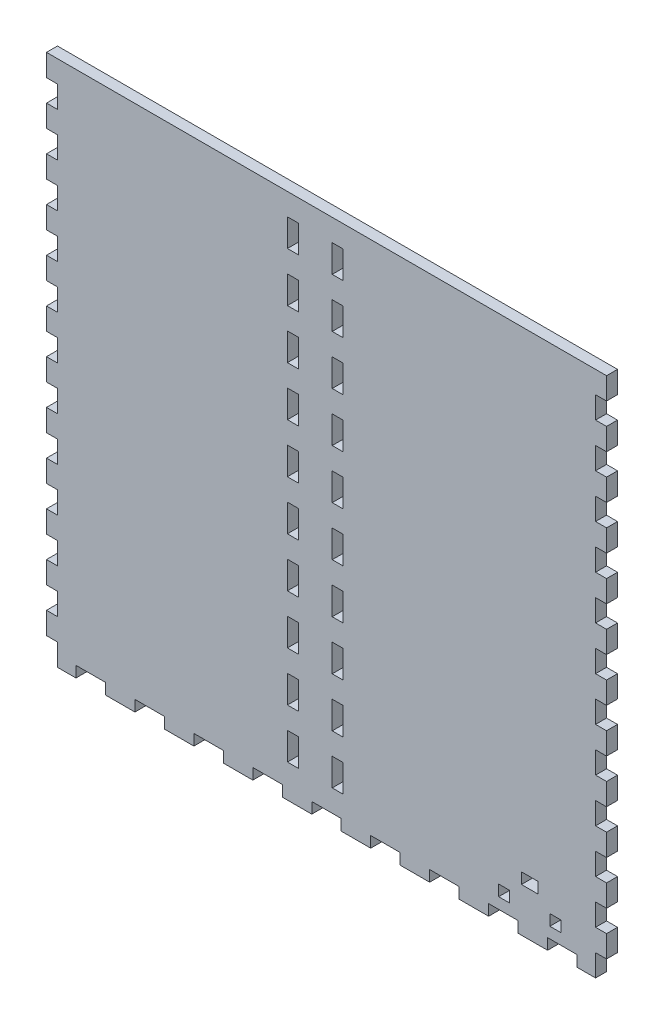
SolidWorks part; units mm, degrees
material "Acrylic (Medium-high impact)"
ref_plane "Front Plane" through (0, 0, 0) normal (0, 0, 1) x (1, 0, 0)
ref_plane "Top Plane" through (0, 0, 0) normal (0, 1, 0) x (1, 0, 0)
ref_plane "Right Plane" through (0, 0, 0) normal (1, 0, 0) x (0, 0, -1)
sketch "Sketch1" plane through (0, 0, 0) normal (0, 1, 0) x (1, 0, 0)
  line L1 (-161.925, 69.85) -> (161.925, 69.85)
  line L2 (-161.925, 69.85) -> (-161.925, -69.85)
  line L3 (-161.925, -69.85) -> (161.925, -69.85)
  line L4 (161.925, 69.85) -> (161.925, -69.85)
  point P4 (-161.925, 0)
  point P6 (0, 69.85)
  dimension "D1" = 139.7
  dimension "D2" = 323.85
extrude "Boss-Extrude1" add sketch "Sketch1" along normal blind 6.35
sketch "Sketch2" plane through (0, 6.35, 0) normal (0, 1, 0) x (1, 0, 0)
  line L0 (161.925, -69.85) -> (161.925, 69.85) construction
  line L1 (-161.925, 69.85) -> (161.925, 69.85)
  line L2 (-161.925, 69.85) -> (-161.925, -69.85)
  line L3 (-161.925, -69.85) -> (161.925, -69.85)
  line L4 (161.925, 69.85) -> (161.925, -69.85)
  line L5 (-161.925, -69.85) -> (161.925, -69.85) construction
  line L7 (-155.575, 63.5) -> (155.575, 63.5)
  line L8 (-155.575, 63.5) -> (-155.575, -63.5)
  line L9 (-155.575, -63.5) -> (155.575, -63.5)
  line L10 (155.575, 63.5) -> (155.575, -63.5)
  point P7 (-155.575, 0)
  point P14 (-161.925, 0)
  point P15 (0, -63.5)
  point P16 (0, -69.85)
  point P17 (155.575, 0)
  point P18 (161.925, 0)
  dimension "D1" = 6.35
  dimension "D2" = 6.35
extrude "Boss-Extrude2" add sketch "Sketch2" along normal blind 298.45
sketch "Sketch3" plane through (0, 0, 69.85) normal (0, 0, 1) x (1, 0, 0)
  line L0 (0, 304.8) -> (0, 0) construction
  line L2 (-155.575, 6.35) -> (155.575, 6.35) construction
  line L4 (-3.302, 283.21) -> (-3.302, 6.35)
  line L5 (-3.302, 6.35) -> (3.302, 6.35)
  line L6 (3.302, 292.354) -> (3.302, 6.35)
  line L7 (3.302, 292.354) -> (-16.256, 292.354)
  line L9 (-5.842, 285.75) -> (-16.256, 285.75)
  line L10 (-16.256, 292.354) -> (-16.256, 285.75)
  line L11 (3.302, 101.6) -> (16.002, 101.6) construction
  line L12 (-161.925, 0) -> (161.925, 0) construction
  line L13 (12.827, 88.9) -> (12.827, 101.6) construction
  line L14 (9.652, 88.9) -> (16.002, 88.9)
  line L15 (9.652, 88.9) -> (9.652, 71.9667)
  line L16 (9.652, 71.9667) -> (16.002, 71.9667)
  line L17 (16.002, 88.9) -> (16.002, 71.9667)
  line L18 (9.652, 42.3333) -> (16.002, 42.3333)
  line L19 (9.652, 42.3333) -> (9.652, 59.2667)
  line L20 (9.652, 59.2667) -> (16.002, 59.2667)
  line L21 (16.002, 42.3333) -> (16.002, 59.2667)
  line L26 (9.652, 29.6333) -> (16.002, 29.6333)
  line L27 (9.652, 29.6333) -> (9.652, 12.7)
  line L28 (9.652, 12.7) -> (16.002, 12.7)
  line L29 (16.002, 29.6333) -> (16.002, 12.7)
  line L30 (12.827, 59.2667) -> (12.827, 71.9667) construction
  line L31 (12.827, 29.6333) -> (12.827, 42.3333) construction
  line L32 (12.827, 12.7) -> (12.827, 0) construction
  line L33 (-161.925, 304.8) -> (161.925, 304.8) construction
  arc A0 (-3.302, 283.21) -> (-5.842, 285.75) centre (-5.842, 283.21) ccw
  point P4 (0, 0)
  point P5 (0, 6.35)
  dimension "D5" = 2.54
  dimension "D1" = 6.604
  dimension "D2" = 12.954
  dimension "D3" = 6.604
  dimension "D4" = 286.004
  dimension "D6" = 101.6
  dimension "D7" = 12.7
  dimension "D8" = 12.7
  dimension "D9" = 6.35
extrude "Door Slot" cut sketch "Sketch3" against normal blind 12.7
sketch "Sketch4" plane through (0, 0, -63.5) normal (0, 0, 1) x (1, 0, 0)
  line L0 (-161.925, 304.8) -> (161.925, 304.8) construction
  line L1 (-22.606, 304.8) -> (-16.256, 304.8)
  line L2 (-22.606, 304.8) -> (-22.606, 6.35)
  line L3 (-22.606, 6.35) -> (-16.256, 6.35)
  line L4 (-16.256, 304.8) -> (-16.256, 6.35)
  line L5 (6.477, 263.525) -> (6.477, 247.65) construction
  line L6 (-16.256, 292.354) -> (-16.256, 285.75) construction
  line L7 (3.302, 304.8) -> (9.652, 304.8)
  line L8 (3.302, 304.8) -> (3.302, 6.35)
  line L9 (3.302, 6.35) -> (9.652, 6.35)
  line L10 (9.652, 304.8) -> (9.652, 6.35)
  line L11 (155.575, 6.35) -> (-155.575, 6.35) construction
  line L12 (3.302, 6.35) -> (3.302, 292.354) construction
  line L13 (-16.256, 304.8) -> (-22.606, 304.8)
  line L14 (-16.256, 304.8) -> (-16.256, 292.1)
  line L15 (-16.256, 292.1) -> (-22.606, 292.1)
  line L16 (-22.606, 304.8) -> (-22.606, 292.1)
  line L17 (-16.256, 276.225) -> (-22.606, 276.225)
  line L18 (-16.256, 276.225) -> (-16.256, 263.525)
  line L19 (-16.256, 263.525) -> (-22.606, 263.525)
  line L20 (-22.606, 276.225) -> (-22.606, 263.525)
  line L21 (-22.606, 6.35) -> (-16.256, 6.35)
  line L22 (-22.606, 6.35) -> (-22.606, 19.05)
  line L23 (-22.606, 19.05) -> (-16.256, 19.05)
  line L24 (-16.256, 6.35) -> (-16.256, 19.05)
  line L25 (-22.606, 34.925) -> (-16.256, 34.925)
  line L26 (-22.606, 34.925) -> (-22.606, 47.625)
  line L27 (-22.606, 47.625) -> (-16.256, 47.625)
  line L28 (-16.256, 34.925) -> (-16.256, 47.625)
  line L29 (-22.606, 92.075) -> (-16.256, 92.075)
  line L30 (-22.606, 92.075) -> (-22.606, 104.775)
  line L31 (-22.606, 104.775) -> (-16.256, 104.775)
  line L32 (-16.256, 92.075) -> (-16.256, 104.775)
  line L33 (-22.606, 149.225) -> (-16.256, 149.225)
  line L34 (-22.606, 149.225) -> (-22.606, 161.925)
  line L35 (-22.606, 161.925) -> (-16.256, 161.925)
  line L36 (-16.256, 149.225) -> (-16.256, 161.925)
  line L37 (-22.606, 177.8) -> (-16.256, 177.8)
  line L38 (-22.606, 177.8) -> (-22.606, 190.5)
  line L39 (-22.606, 190.5) -> (-16.256, 190.5)
  line L40 (-16.256, 177.8) -> (-16.256, 190.5)
  line L41 (-22.606, 206.375) -> (-16.256, 206.375)
  line L42 (-22.606, 206.375) -> (-22.606, 219.075)
  line L43 (-22.606, 219.075) -> (-16.256, 219.075)
  line L44 (-16.256, 206.375) -> (-16.256, 219.075)
  line L45 (-22.606, 234.95) -> (-16.256, 234.95)
  line L46 (-22.606, 234.95) -> (-22.606, 247.65)
  line L47 (-22.606, 247.65) -> (-16.256, 247.65)
  line L48 (-16.256, 234.95) -> (-16.256, 247.65)
  line L49 (-16.256, 133.35) -> (-22.606, 133.35)
  line L50 (-16.256, 133.35) -> (-16.256, 120.65)
  line L51 (-16.256, 120.65) -> (-22.606, 120.65)
  line L52 (-22.606, 133.35) -> (-22.606, 120.65)
  line L53 (-16.256, 76.2) -> (-22.606, 76.2)
  line L54 (-16.256, 76.2) -> (-16.256, 63.5)
  line L55 (-16.256, 63.5) -> (-22.606, 63.5)
  line L56 (-22.606, 76.2) -> (-22.606, 63.5)
  line L57 (-19.431, 304.8) -> (-19.431, 292.1) construction
  line L58 (-19.431, 292.1) -> (-19.431, 276.225) construction
  line L59 (-19.431, 276.225) -> (-19.431, 263.525) construction
  line L60 (-19.431, 247.65) -> (-19.431, 234.95) construction
  line L61 (-19.431, 234.95) -> (-19.431, 219.075) construction
  line L62 (-19.431, 219.075) -> (-19.431, 206.375) construction
  line L63 (-19.431, 206.375) -> (-19.431, 190.5) construction
  line L64 (-19.431, 190.5) -> (-19.431, 177.8) construction
  line L65 (-19.431, 177.8) -> (-19.431, 161.925) construction
  line L66 (-19.431, 161.925) -> (-19.431, 149.225) construction
  line L67 (-19.431, 133.35) -> (-19.431, 120.65) construction
  line L68 (-19.431, 120.65) -> (-19.431, 104.775) construction
  line L69 (-19.431, 104.775) -> (-19.431, 92.075) construction
  line L70 (-19.431, 92.075) -> (-19.431, 76.2) construction
  line L71 (-19.431, 76.2) -> (-19.431, 63.5) construction
  line L72 (-19.431, 63.5) -> (-19.431, 47.625) construction
  line L73 (-19.431, 47.625) -> (-19.431, 34.925) construction
  line L74 (-19.431, 34.925) -> (-19.431, 19.05) construction
  line L75 (-19.431, 19.05) -> (-19.431, 6.35) construction
  line L76 (-19.431, 149.225) -> (-19.431, 133.35) construction
  line L77 (-19.431, 263.525) -> (-19.431, 247.65) construction
  line L78 (-6.477, 304.8) -> (-6.477, 0) construction
  line L79 (161.925, 304.8) -> (-161.925, 304.8) construction
  line L80 (161.925, 0) -> (-161.925, 0) construction
  line L81 (-6.477, 8.3493) -> (3.302, 8.3493) construction
  line L82 (-6.477, 8.3493) -> (-16.256, 8.3493) construction
  line L83 (6.477, 149.225) -> (6.477, 133.35) construction
  line L84 (6.477, 19.05) -> (6.477, 6.35) construction
  line L85 (6.477, 34.925) -> (6.477, 19.05) construction
  line L86 (6.477, 47.625) -> (6.477, 34.925) construction
  line L87 (6.477, 63.5) -> (6.477, 47.625) construction
  line L88 (6.477, 76.2) -> (6.477, 63.5) construction
  line L89 (6.477, 92.075) -> (6.477, 76.2) construction
  line L90 (6.477, 104.775) -> (6.477, 92.075) construction
  line L91 (6.477, 120.65) -> (6.477, 104.775) construction
  line L92 (6.477, 133.35) -> (6.477, 120.65) construction
  line L93 (6.477, 161.925) -> (6.477, 149.225) construction
  line L94 (6.477, 177.8) -> (6.477, 161.925) construction
  line L95 (6.477, 190.5) -> (6.477, 177.8) construction
  line L96 (6.477, 206.375) -> (6.477, 190.5) construction
  line L97 (6.477, 219.075) -> (6.477, 206.375) construction
  line L98 (6.477, 234.95) -> (6.477, 219.075) construction
  line L99 (6.477, 247.65) -> (6.477, 234.95) construction
  line L100 (6.477, 276.225) -> (6.477, 263.525) construction
  line L101 (6.477, 292.1) -> (6.477, 276.225) construction
  line L102 (6.477, 304.8) -> (6.477, 292.1) construction
  line L103 (9.652, 76.2) -> (9.652, 63.5)
  line L104 (3.302, 63.5) -> (9.652, 63.5)
  line L105 (3.302, 76.2) -> (3.302, 63.5)
  line L106 (3.302, 76.2) -> (9.652, 76.2)
  line L107 (9.652, 133.35) -> (9.652, 120.65)
  line L108 (3.302, 120.65) -> (9.652, 120.65)
  line L109 (3.302, 133.35) -> (3.302, 120.65)
  line L110 (3.302, 133.35) -> (9.652, 133.35)
  line L111 (3.302, 234.95) -> (3.302, 247.65)
  line L112 (9.652, 247.65) -> (3.302, 247.65)
  line L113 (9.652, 234.95) -> (9.652, 247.65)
  line L114 (9.652, 234.95) -> (3.302, 234.95)
  line L115 (3.302, 206.375) -> (3.302, 219.075)
  line L116 (9.652, 219.075) -> (3.302, 219.075)
  line L117 (9.652, 206.375) -> (9.652, 219.075)
  line L118 (9.652, 206.375) -> (3.302, 206.375)
  line L119 (3.302, 177.8) -> (3.302, 190.5)
  line L120 (9.652, 190.5) -> (3.302, 190.5)
  line L121 (9.652, 177.8) -> (9.652, 190.5)
  line L122 (9.652, 177.8) -> (3.302, 177.8)
  line L123 (3.302, 149.225) -> (3.302, 161.925)
  line L124 (9.652, 161.925) -> (3.302, 161.925)
  line L125 (9.652, 149.225) -> (9.652, 161.925)
  line L126 (9.652, 149.225) -> (3.302, 149.225)
  line L127 (3.302, 92.075) -> (3.302, 104.775)
  line L128 (9.652, 104.775) -> (3.302, 104.775)
  line L129 (9.652, 92.075) -> (9.652, 104.775)
  line L130 (9.652, 92.075) -> (3.302, 92.075)
  line L131 (3.302, 34.925) -> (3.302, 47.625)
  line L132 (9.652, 47.625) -> (3.302, 47.625)
  line L133 (9.652, 34.925) -> (9.652, 47.625)
  line L134 (9.652, 34.925) -> (3.302, 34.925)
  line L135 (3.302, 6.35) -> (3.302, 19.05)
  line L136 (9.652, 19.05) -> (3.302, 19.05)
  line L137 (9.652, 6.35) -> (9.652, 19.05)
  line L138 (9.652, 6.35) -> (3.302, 6.35)
  line L139 (9.652, 276.225) -> (9.652, 263.525)
  line L140 (3.302, 263.525) -> (9.652, 263.525)
  line L141 (3.302, 276.225) -> (3.302, 263.525)
  line L142 (3.302, 276.225) -> (9.652, 276.225)
  line L143 (9.652, 304.8) -> (9.652, 292.1)
  line L144 (3.302, 292.1) -> (9.652, 292.1)
  line L145 (3.302, 304.8) -> (3.302, 292.1)
  line L146 (3.302, 304.8) -> (9.652, 304.8)
  line L147 (3.302, 304.8) -> (3.302, 6.35)
  line L148 (9.652, 6.35) -> (3.302, 6.35)
  line L149 (9.652, 304.8) -> (9.652, 6.35)
  line L150 (9.652, 304.8) -> (3.302, 304.8)
  point P14 (-16.256, 289.052)
  dimension "D1" = 6.35
  dimension "D2" = 12.7
extrude "Door Guide Holes" cut sketch "Sketch4" against normal up to next contours L17 L4 L15 L2 | L2 L47 L4 L19 | L45 L2 L43 L4 | L41 L2 L39 L4 | L37 L2 L35 L4 | L49 L4 L33 L2 | L4 L51 L2 L31 | L53 L4 L29 L2 | L4 L55 L2 L27 | L25 L2 L23 L4
ref_plane "Plane1" through (-6.477, 0, 0) normal (-1, 0, 0) x (0, 0, 1)
mirror "Mirror1" about plane through (-6.477, 0, 0) normal (-1, 0, 0) of "Door Guide Holes"
sketch "Lever Holes" plane through (0, 0, 69.85) normal (0, 0, 1) x (1, 0, 0)
  line L0 (112.7125, 31.75) -> (122.3645, 31.75)
  line L1 (112.7125, 31.75) -> (112.7125, 25.4)
  line L2 (112.7125, 25.4) -> (122.3645, 25.4)
  line L3 (122.3645, 31.75) -> (122.3645, 25.4)
  line L4 (99.568, 19.05) -> (105.918, 19.05)
  line L5 (99.568, 19.05) -> (99.568, 12.7)
  line L6 (99.568, 12.7) -> (105.918, 12.7)
  line L7 (105.918, 19.05) -> (105.918, 12.7)
  line L8 (129.159, 19.05) -> (135.509, 19.05)
  line L9 (129.159, 19.05) -> (129.159, 12.7)
  line L10 (129.159, 12.7) -> (135.509, 12.7)
  line L11 (135.509, 19.05) -> (135.509, 12.7)
  line L12 (105.918, 15.875) -> (129.159, 15.875) construction
  line L13 (-161.925, 0) -> (161.925, 0) construction
  line L14 (3.302, 6.35) -> (155.575, 6.35) construction
  line L15 (155.575, 6.35) -> (-155.575, 6.35) construction
  point P12 (117.5385, 15.875)
  point P13 (117.5385, 25.4)
  point P14 (107.3846, 25.4)
  point P24 (79.4385, 6.35)
  dimension "D1" = 9.652
  dimension "D2" = 6.35
  dimension "D3" = 6.35
  dimension "D4" = 6.35
  dimension "D5" = 23.241
  dimension "D6" = 25.4
  dimension "D7" = 12.7
  dimension "D8" = 38.1
extrude "Cut-Extrude1" cut sketch "Lever Holes" against normal through all
sketch "Sketch7" plane through (161.925, 0, 0) normal (1, 0, 0) x (0, 0, -1)
  line L0 (-37.211, 92.583) -> (37.211, 92.583)
  line L1 (-37.211, 92.583) -> (-37.211, 18.161)
  line L2 (-37.211, 18.161) -> (37.211, 18.161)
  line L3 (37.211, 92.583) -> (37.211, 18.161)
  line L4 (-69.85, 0) -> (69.85, 0) construction
  circle A0 centre (0, 55.372) radius 26.9875
  circle A1 centre (-37.211, 92.583) radius 3.175
  circle A2 centre (37.211, 92.583) radius 3.175
  circle A3 centre (-37.211, 18.161) radius 3.175
  circle A4 centre (37.211, 18.161) radius 3.175
  point P9 (0, 18.161)
  point P10 (-37.211, 55.372)
  dimension "D3" = 53.975
  dimension "D4" = 6.35
  dimension "D1" = 74.422
  dimension "D2" = 55.372
extrude "Cut-Extrude2" cut sketch "Sketch7" against normal up to next contours A0 | L0 A1 L1 | L1 A1 L0 | L3 A2 L0 | L0 A2 L3 | L2 A3 L1 | L1 A3 L2 | L2 A4 L3 | L3 A4 L2
sketch "Sketch8" plane through (-161.925, 0, 0) normal (-1, 0, 0) x (0, 0, 1)
  line L0 (-69.85, 0) -> (69.85, 0) construction
  circle A0 centre (0, 19.05) radius 3.175
  point P6 (0, 0)
  dimension "D1" = 6.35
  dimension "D2" = 19.05
extrude "Cut-Extrude3" cut sketch "Sketch8" against normal up to next
sketch "Bottom" plane through (0, 0, 0) normal (0, -1, 0) x (1, 0, 0)
  line L0 (-155.575, 63.5) -> (155.575, 63.5) construction
  line L1 (-161.925, 69.85) -> (-144.8803, 69.85)
  line L2 (-161.925, 69.85) -> (-161.925, 63.5)
  line L3 (-161.925, 63.5) -> (-144.8803, 63.5)
  line L4 (-144.8803, 69.85) -> (-144.8803, 63.5)
  line L5 (-144.8803, 69.85) -> (-127.8355, 69.85)
  line L6 (-144.8803, 69.85) -> (-144.8803, 63.5)
  line L7 (-144.8803, 63.5) -> (-127.8355, 63.5)
  line L8 (-127.8355, 69.85) -> (-127.8355, 63.5)
  line L9 (-127.8355, 69.85) -> (-110.7908, 69.85)
  line L10 (-127.8355, 69.85) -> (-127.8355, 63.5)
  line L11 (-127.8355, 63.5) -> (-110.7908, 63.5)
  line L12 (-110.7908, 69.85) -> (-110.7908, 63.5)
  line L13 (-110.7908, 69.85) -> (-93.7461, 69.85)
  line L14 (-110.7908, 69.85) -> (-110.7908, 63.5)
  line L15 (-110.7908, 63.5) -> (-93.7461, 63.5)
  line L16 (-93.7461, 69.85) -> (-93.7461, 63.5)
  line L17 (-161.925, 69.85) -> (161.925, 69.85) construction
  line L18 (-16.256, 63.5) -> (3.302, 63.5) construction
  line L19 (-93.7461, 69.85) -> (-76.7013, 69.85)
  line L20 (-93.7461, 69.85) -> (-93.7461, 63.5)
  line L21 (-93.7461, 63.5) -> (-76.7013, 63.5)
  line L22 (-76.7013, 69.85) -> (-76.7013, 63.5)
  line L23 (-76.7013, 69.85) -> (-59.6566, 69.85)
  line L24 (-76.7013, 69.85) -> (-76.7013, 63.5)
  line L25 (-76.7013, 63.5) -> (-59.6566, 63.5)
  line L26 (-59.6566, 69.85) -> (-59.6566, 63.5)
  line L27 (-59.6566, 69.85) -> (-42.6118, 69.85)
  line L28 (-59.6566, 69.85) -> (-59.6566, 63.5)
  line L29 (-59.6566, 63.5) -> (-42.6118, 63.5)
  line L30 (-42.6118, 69.85) -> (-42.6118, 63.5)
  line L31 (-42.6118, 69.85) -> (-25.5671, 69.85)
  line L32 (-42.6118, 69.85) -> (-42.6118, 63.5)
  line L33 (-42.6118, 63.5) -> (-25.5671, 63.5)
  line L34 (-25.5671, 69.85) -> (-25.5671, 63.5)
  line L36 (-25.5671, 69.85) -> (-8.5224, 69.85)
  line L37 (-25.5671, 69.85) -> (-25.5671, 63.5)
  line L38 (-25.5671, 63.5) -> (-8.5224, 63.5)
  line L39 (-8.5224, 69.85) -> (-8.5224, 63.5)
  line L40 (-8.5224, 69.85) -> (8.5224, 69.85)
  line L41 (-8.5224, 69.85) -> (-8.5224, 63.5)
  line L42 (-8.5224, 63.5) -> (8.5224, 63.5)
  line L43 (8.5224, 69.85) -> (8.5224, 63.5)
  line L44 (8.5224, 69.85) -> (25.5671, 69.85)
  line L45 (8.5224, 69.85) -> (8.5224, 63.5)
  line L46 (8.5224, 63.5) -> (25.5671, 63.5)
  line L47 (25.5671, 69.85) -> (25.5671, 63.5)
  line L48 (25.5671, 69.85) -> (42.6118, 69.85)
  line L49 (25.5671, 69.85) -> (25.5671, 63.5)
  line L50 (25.5671, 63.5) -> (42.6118, 63.5)
  line L51 (42.6118, 69.85) -> (42.6118, 63.5)
  line L52 (42.6118, 69.85) -> (59.6566, 69.85)
  line L53 (42.6118, 69.85) -> (42.6118, 63.5)
  line L54 (42.6118, 63.5) -> (59.6566, 63.5)
  line L55 (59.6566, 69.85) -> (59.6566, 63.5)
  line L56 (59.6566, 69.85) -> (76.7013, 69.85)
  line L57 (59.6566, 69.85) -> (59.6566, 63.5)
  line L58 (59.6566, 63.5) -> (76.7013, 63.5)
  line L59 (76.7013, 69.85) -> (76.7013, 63.5)
  line L60 (76.7013, 69.85) -> (93.7461, 69.85)
  line L61 (76.7013, 69.85) -> (76.7013, 63.5)
  line L62 (76.7013, 63.5) -> (93.7461, 63.5)
  line L63 (93.7461, 69.85) -> (93.7461, 63.5)
  line L64 (93.7461, 69.85) -> (110.7908, 69.85)
  line L65 (93.7461, 69.85) -> (93.7461, 63.5)
  line L66 (93.7461, 63.5) -> (110.7908, 63.5)
  line L67 (110.7908, 69.85) -> (110.7908, 63.5)
  line L68 (110.7908, 69.85) -> (127.8355, 69.85)
  line L69 (110.7908, 69.85) -> (110.7908, 63.5)
  line L70 (110.7908, 63.5) -> (127.8355, 63.5)
  line L71 (127.8355, 69.85) -> (127.8355, 63.5)
  line L72 (127.8355, 69.85) -> (144.8803, 69.85)
  line L73 (127.8355, 69.85) -> (127.8355, 63.5)
  line L74 (127.8355, 63.5) -> (144.8803, 63.5)
  line L75 (144.8803, 69.85) -> (144.8803, 63.5)
  line L76 (-155.575, -63.5) -> (-155.575, 63.5) construction
  line L77 (-161.925, 69.85) -> (-155.575, 69.85)
  line L78 (-161.925, 69.85) -> (-161.925, 57.15)
  line L79 (-161.925, 57.15) -> (-155.575, 57.15)
  line L80 (-155.575, 69.85) -> (-155.575, 57.15)
  line L82 (-161.925, 57.15) -> (-155.575, 57.15)
  line L83 (-161.925, 57.15) -> (-161.925, 44.45)
  line L84 (-161.925, 44.45) -> (-155.575, 44.45)
  line L85 (-155.575, 57.15) -> (-155.575, 44.45)
  line L86 (-161.925, 44.45) -> (-155.575, 44.45)
  line L87 (-161.925, 44.45) -> (-161.925, 31.75)
  line L88 (-161.925, 31.75) -> (-155.575, 31.75)
  line L89 (-155.575, 44.45) -> (-155.575, 31.75)
  line L90 (-161.925, 31.75) -> (-155.575, 31.75)
  line L91 (-161.925, 31.75) -> (-161.925, 19.05)
  line L92 (-161.925, 19.05) -> (-155.575, 19.05)
  line L93 (-155.575, 31.75) -> (-155.575, 19.05)
  line L94 (-161.925, 19.05) -> (-155.575, 19.05)
  line L95 (-161.925, 19.05) -> (-161.925, 6.35)
  line L96 (-161.925, 6.35) -> (-155.575, 6.35)
  line L97 (-155.575, 19.05) -> (-155.575, 6.35)
  line L98 (-161.925, 6.35) -> (-155.575, 6.35)
  line L99 (-161.925, 6.35) -> (-161.925, -6.35)
  line L100 (-161.925, -6.35) -> (-155.575, -6.35)
  line L101 (-155.575, 6.35) -> (-155.575, -6.35)
  line L102 (-161.925, -6.35) -> (-155.575, -6.35)
  line L103 (-161.925, -6.35) -> (-161.925, -19.05)
  line L104 (-161.925, -19.05) -> (-155.575, -19.05)
  line L105 (-155.575, -6.35) -> (-155.575, -19.05)
  line L106 (-161.925, -19.05) -> (-155.575, -19.05)
  line L107 (-161.925, -19.05) -> (-161.925, -31.75)
  line L108 (-161.925, -31.75) -> (-155.575, -31.75)
  line L109 (-155.575, -19.05) -> (-155.575, -31.75)
  line L110 (-161.925, -31.75) -> (-155.575, -31.75)
  line L111 (-161.925, -31.75) -> (-161.925, -44.45)
  line L112 (-161.925, -44.45) -> (-155.575, -44.45)
  line L113 (-155.575, -31.75) -> (-155.575, -44.45)
  line L114 (-161.925, -44.45) -> (-155.575, -44.45)
  line L115 (-161.925, -44.45) -> (-161.925, -57.15)
  line L116 (-161.925, -57.15) -> (-155.575, -57.15)
  line L117 (-155.575, -44.45) -> (-155.575, -57.15)
  line L118 (161.925, 69.85) -> (161.925, -69.85) construction
  line L119 (144.8803, 69.85) -> (161.925, 69.85)
  line L120 (144.8803, 69.85) -> (144.8803, 63.5)
  line L121 (144.8803, 63.5) -> (161.925, 63.5)
  line L122 (161.925, 69.85) -> (161.925, 63.5)
  line L123 (161.925, -69.85) -> (-161.925, -69.85) construction
  line L124 (-161.925, -57.15) -> (-155.575, -57.15)
  line L125 (-161.925, -57.15) -> (-161.925, -69.85)
  line L126 (-161.925, -69.85) -> (-155.575, -69.85)
  line L127 (-155.575, -57.15) -> (-155.575, -69.85)
  line L128 (167.64, 0) -> (-167.64, 0) construction
  line L129 (161.925, -69.85) -> (161.925, -63.5)
  line L130 (144.8803, -63.5) -> (161.925, -63.5)
  line L131 (144.8803, -69.85) -> (161.925, -69.85)
  line L132 (144.8803, -69.85) -> (144.8803, -63.5)
  line L133 (127.8355, -63.5) -> (144.8803, -63.5)
  line L134 (127.8355, -69.85) -> (144.8803, -69.85)
  line L135 (127.8355, -69.85) -> (127.8355, -63.5)
  line L136 (110.7908, -63.5) -> (127.8355, -63.5)
  line L137 (110.7908, -69.85) -> (127.8355, -69.85)
  line L138 (110.7908, -69.85) -> (110.7908, -63.5)
  line L139 (93.7461, -63.5) -> (110.7908, -63.5)
  line L140 (93.7461, -69.85) -> (110.7908, -69.85)
  line L141 (93.7461, -69.85) -> (93.7461, -63.5)
  line L142 (76.7013, -63.5) -> (93.7461, -63.5)
  line L143 (76.7013, -69.85) -> (93.7461, -69.85)
  line L144 (59.6566, -63.5) -> (76.7013, -63.5)
  line L145 (76.7013, -69.85) -> (76.7013, -63.5)
  line L146 (59.6566, -69.85) -> (76.7013, -69.85)
  line L147 (59.6566, -69.85) -> (59.6566, -63.5)
  line L148 (42.6118, -63.5) -> (59.6566, -63.5)
  line L149 (42.6118, -69.85) -> (59.6566, -69.85)
  line L150 (42.6118, -69.85) -> (42.6118, -63.5)
  line L151 (25.5671, -63.5) -> (42.6118, -63.5)
  line L152 (25.5671, -69.85) -> (42.6118, -69.85)
  line L153 (25.5671, -69.85) -> (25.5671, -63.5)
  line L154 (8.5224, -69.85) -> (25.5671, -69.85)
  line L155 (8.5224, -63.5) -> (25.5671, -63.5)
  line L156 (8.5224, -69.85) -> (8.5224, -63.5)
  line L157 (-8.5224, -63.5) -> (8.5224, -63.5)
  line L158 (-8.5224, -69.85) -> (8.5224, -69.85)
  line L159 (-25.5671, -63.5) -> (-8.5224, -63.5)
  line L160 (-8.5224, -69.85) -> (-8.5224, -63.5)
  line L161 (-25.5671, -69.85) -> (-8.5224, -69.85)
  line L162 (-25.5671, -69.85) -> (-25.5671, -63.5)
  line L163 (-42.6118, -63.5) -> (-25.5671, -63.5)
  line L164 (-42.6118, -69.85) -> (-25.5671, -69.85)
  line L165 (-42.6118, -69.85) -> (-42.6118, -63.5)
  line L166 (-59.6566, -63.5) -> (-42.6118, -63.5)
  line L167 (-59.6566, -69.85) -> (-42.6118, -69.85)
  line L168 (-59.6566, -69.85) -> (-59.6566, -63.5)
  line L169 (-76.7013, -69.85) -> (-59.6566, -69.85)
  line L170 (-76.7013, -63.5) -> (-59.6566, -63.5)
  line L171 (-93.7461, -63.5) -> (-76.7013, -63.5)
  line L172 (-76.7013, -69.85) -> (-76.7013, -63.5)
  line L173 (-93.7461, -69.85) -> (-76.7013, -69.85)
  line L174 (-110.7908, -69.85) -> (-93.7461, -69.85)
  line L175 (-110.7908, -63.5) -> (-93.7461, -63.5)
  line L176 (-93.7461, -69.85) -> (-93.7461, -63.5)
  line L177 (-127.8355, -69.85) -> (-127.8355, -63.5)
  line L178 (-127.8355, -69.85) -> (-110.7908, -69.85)
  line L179 (-110.7908, -69.85) -> (-110.7908, -63.5)
  line L180 (-127.8355, -63.5) -> (-110.7908, -63.5)
  line L181 (-144.8803, -63.5) -> (-127.8355, -63.5)
  line L182 (-144.8803, -69.85) -> (-127.8355, -69.85)
  line L183 (-144.8803, -69.85) -> (-144.8803, -63.5)
  line L184 (-161.925, -69.85) -> (-144.8803, -69.85)
  line L185 (-161.925, -69.85) -> (-161.925, -63.5)
  line L186 (-161.925, -63.5) -> (-144.8803, -63.5)
  line L187 (0, -76.835) -> (0, 76.835) construction
  line L188 (161.925, -69.85) -> (155.575, -69.85)
  line L189 (155.575, -57.15) -> (155.575, -69.85)
  line L190 (161.925, -57.15) -> (161.925, -69.85)
  line L191 (161.925, -57.15) -> (155.575, -57.15)
  line L192 (155.575, -44.45) -> (155.575, -57.15)
  line L193 (161.925, -44.45) -> (161.925, -57.15)
  line L194 (161.925, -44.45) -> (155.575, -44.45)
  line L195 (155.575, -31.75) -> (155.575, -44.45)
  line L196 (161.925, -31.75) -> (161.925, -44.45)
  line L197 (161.925, -31.75) -> (155.575, -31.75)
  line L198 (161.925, -19.05) -> (161.925, -31.75)
  line L199 (155.575, -19.05) -> (155.575, -31.75)
  line L200 (155.575, -6.35) -> (155.575, -19.05)
  line L201 (161.925, -6.35) -> (161.925, -19.05)
  line L202 (161.925, -19.05) -> (155.575, -19.05)
  line L203 (161.925, -6.35) -> (155.575, -6.35)
  line L204 (155.575, 6.35) -> (155.575, -6.35)
  line L205 (161.925, 6.35) -> (161.925, -6.35)
  line L206 (161.925, 6.35) -> (155.575, 6.35)
  line L207 (155.575, 19.05) -> (155.575, 6.35)
  line L208 (161.925, 19.05) -> (161.925, 6.35)
  line L209 (161.925, 19.05) -> (155.575, 19.05)
  line L210 (161.925, 31.75) -> (155.575, 31.75)
  line L211 (161.925, 44.45) -> (155.575, 44.45)
  line L212 (161.925, 57.15) -> (155.575, 57.15)
  line L213 (155.575, 31.75) -> (155.575, 19.05)
  line L214 (161.925, 31.75) -> (161.925, 19.05)
  line L215 (155.575, 44.45) -> (155.575, 31.75)
  line L216 (161.925, 44.45) -> (161.925, 31.75)
  line L217 (155.575, 57.15) -> (155.575, 44.45)
  line L218 (161.925, 57.15) -> (161.925, 44.45)
  line L219 (155.575, 69.85) -> (155.575, 57.15)
  line L220 (161.925, 69.85) -> (161.925, 57.15)
sketch "Front/Back" plane through (0, 0, 69.85) normal (0, 0, 1) x (1, 0, 0)
  line L0 (-155.575, 6.35) -> (-3.302, 6.35) construction
  line L1 (-161.925, 0) -> (-144.8803, 0)
  line L2 (-161.925, 0) -> (-161.925, 6.35)
  line L3 (-161.925, 6.35) -> (-144.8803, 6.35)
  line L4 (-144.8803, 0) -> (-144.8803, 6.35)
  line L5 (-161.925, 0) -> (161.925, 0) construction
  line L6 (-127.8355, 0) -> (-110.7908, 0) construction
  line L7 (-144.8803, 6.35) -> (-127.8355, 6.35)
  line L8 (-144.8803, 6.35) -> (-144.8803, 0)
  line L9 (-144.8803, 0) -> (-127.8355, 0)
  line L10 (-127.8355, 6.35) -> (-127.8355, 0)
  line L11 (-93.7461, 0) -> (-76.7013, 0) construction
  line L12 (-127.8355, 6.35) -> (-110.7908, 6.35)
  line L13 (-127.8355, 6.35) -> (-127.8355, 0)
  line L14 (-127.8355, 0) -> (-110.7908, 0)
  line L15 (-110.7908, 6.35) -> (-110.7908, 0)
  line L16 (-110.7908, 6.35) -> (-93.7461, 6.35)
  line L17 (-110.7908, 6.35) -> (-110.7908, 0)
  line L18 (-110.7908, 0) -> (-93.7461, 0)
  line L19 (-93.7461, 6.35) -> (-93.7461, 0)
  line L20 (-76.7013, 0) -> (-59.6566, 0) construction
  line L21 (-93.7461, 6.35) -> (-76.7013, 6.35)
  line L22 (-93.7461, 6.35) -> (-93.7461, 0)
  line L23 (-93.7461, 0) -> (-76.7013, 0)
  line L24 (-76.7013, 6.35) -> (-76.7013, 0)
  line L25 (-76.7013, 6.35) -> (-59.6566, 6.35)
  line L26 (-76.7013, 6.35) -> (-76.7013, 0)
  line L27 (-76.7013, 0) -> (-59.6566, 0)
  line L28 (-59.6566, 6.35) -> (-59.6566, 0)
  line L29 (-59.6566, 0) -> (-42.6118, 0) construction
  line L30 (-59.6566, 6.35) -> (-42.6118, 6.35)
  line L31 (-59.6566, 6.35) -> (-59.6566, 0)
  line L32 (-59.6566, 0) -> (-42.6118, 0)
  line L33 (-42.6118, 6.35) -> (-42.6118, 0)
  line L34 (-25.5671, 0) -> (-8.5224, 0) construction
  line L35 (-42.6118, 6.35) -> (-25.5671, 6.35)
  line L36 (-42.6118, 6.35) -> (-42.6118, 0)
  line L37 (-42.6118, 0) -> (-25.5671, 0)
  line L38 (-25.5671, 6.35) -> (-25.5671, 0)
  line L39 (8.5224, 0) -> (25.5671, 0) construction
  line L40 (-25.5671, 6.35) -> (-8.5224, 6.35)
  line L41 (-25.5671, 6.35) -> (-25.5671, 0)
  line L42 (-25.5671, 0) -> (-8.5224, 0)
  line L43 (-8.5224, 6.35) -> (-8.5224, 0)
  line L44 (-8.5224, 6.35) -> (8.5224, 6.35)
  line L45 (-8.5224, 6.35) -> (-8.5224, 0)
  line L46 (-8.5224, 0) -> (8.5224, 0)
  line L47 (8.5224, 6.35) -> (8.5224, 0)
  line L48 (8.5224, 0) -> (25.5671, 0) construction
  line L49 (42.6118, 0) -> (59.6566, 0) construction
  line L50 (8.5224, 6.35) -> (25.5671, 6.35)
  line L51 (8.5224, 6.35) -> (8.5224, 0)
  line L52 (8.5224, 0) -> (25.5671, 0)
  line L53 (25.5671, 6.35) -> (25.5671, 0)
  line L54 (25.5671, 6.35) -> (42.6118, 6.35)
  line L55 (25.5671, 6.35) -> (25.5671, 0)
  line L56 (25.5671, 0) -> (42.6118, 0)
  line L57 (42.6118, 6.35) -> (42.6118, 0)
  line L58 (76.7013, 0) -> (93.7461, 0) construction
  line L59 (42.6118, 6.35) -> (59.6566, 6.35)
  line L60 (42.6118, 6.35) -> (42.6118, 0)
  line L61 (42.6118, 0) -> (59.6566, 0)
  line L62 (59.6566, 6.35) -> (59.6566, 0)
  line L63 (59.6566, 6.35) -> (76.7013, 6.35)
  line L64 (59.6566, 6.35) -> (59.6566, 0)
  line L65 (59.6566, 0) -> (76.7013, 0)
  line L66 (76.7013, 6.35) -> (76.7013, 0)
  line L67 (59.6566, 0) -> (76.7013, 0) construction
  line L68 (110.7908, 0) -> (127.8355, 0) construction
  line L69 (76.7013, 6.35) -> (93.7461, 6.35)
  line L70 (76.7013, 6.35) -> (76.7013, 0)
  line L71 (76.7013, 0) -> (93.7461, 0)
  line L72 (93.7461, 6.35) -> (93.7461, 0)
  line L73 (93.7461, 6.35) -> (110.7908, 6.35)
  line L74 (93.7461, 6.35) -> (93.7461, 0)
  line L75 (93.7461, 0) -> (110.7908, 0)
  line L76 (110.7908, 6.35) -> (110.7908, 0)
  line L77 (127.8355, 0) -> (144.8803, 0) construction
  line L78 (110.7908, 6.35) -> (127.8355, 6.35)
  line L79 (110.7908, 6.35) -> (110.7908, 0)
  line L80 (110.7908, 0) -> (127.8355, 0)
  line L81 (127.8355, 6.35) -> (127.8355, 0)
  line L82 (127.8355, 0) -> (144.8803, 0) construction
  line L84 (127.8355, 6.35) -> (144.8803, 6.35)
  line L85 (127.8355, 6.35) -> (127.8355, 0)
  line L86 (127.8355, 0) -> (144.8803, 0)
  line L87 (144.8803, 6.35) -> (144.8803, 0)
  line L88 (144.8803, 6.35) -> (161.925, 6.35)
  line L89 (144.8803, 6.35) -> (144.8803, 0)
  line L90 (144.8803, 0) -> (161.925, 0)
  line L91 (161.925, 6.35) -> (161.925, 0)
  line L92 (-155.575, 304.8) -> (-155.575, 6.35) construction
  line L93 (-161.925, 0) -> (-155.575, 0)
  line L94 (-161.925, 0) -> (-161.925, 12.7)
  line L95 (-161.925, 12.7) -> (-155.575, 12.7)
  line L96 (-155.575, 0) -> (-155.575, 12.7)
  line L97 (-161.925, 304.8) -> (-161.925, 0) construction
  line L98 (-161.925, 12.7) -> (-155.575, 12.7)
  line L99 (-161.925, 12.7) -> (-161.925, 25.4)
  line L100 (-161.925, 25.4) -> (-155.575, 25.4)
  line L101 (-155.575, 12.7) -> (-155.575, 25.4)
  line L102 (-161.925, 25.4) -> (-155.575, 25.4)
  line L103 (-161.925, 25.4) -> (-161.925, 38.1)
  line L104 (-161.925, 38.1) -> (-155.575, 38.1)
  line L105 (-155.575, 25.4) -> (-155.575, 38.1)
  line L106 (-161.925, 38.1) -> (-155.575, 38.1)
  line L107 (-161.925, 38.1) -> (-161.925, 50.8)
  line L108 (-161.925, 50.8) -> (-155.575, 50.8)
  line L109 (-155.575, 38.1) -> (-155.575, 50.8)
  line L110 (-161.925, 50.8) -> (-155.575, 50.8)
  line L111 (-161.925, 50.8) -> (-161.925, 63.5)
  line L112 (-161.925, 63.5) -> (-155.575, 63.5)
  line L113 (-155.575, 50.8) -> (-155.575, 63.5)
  line L114 (-161.925, 63.5) -> (-155.575, 63.5)
  line L115 (-161.925, 63.5) -> (-161.925, 76.2)
  line L116 (-161.925, 76.2) -> (-155.575, 76.2)
  line L117 (-155.575, 63.5) -> (-155.575, 76.2)
  line L118 (-161.925, 76.2) -> (-155.575, 76.2)
  line L119 (-161.925, 76.2) -> (-161.925, 88.9)
  line L120 (-161.925, 88.9) -> (-155.575, 88.9)
  line L121 (-155.575, 76.2) -> (-155.575, 88.9)
  line L122 (-161.925, 88.9) -> (-155.575, 88.9)
  line L123 (-161.925, 88.9) -> (-161.925, 101.6)
  line L124 (-161.925, 101.6) -> (-155.575, 101.6)
  line L125 (-155.575, 88.9) -> (-155.575, 101.6)
  line L126 (-161.925, 101.6) -> (-155.575, 101.6)
  line L127 (-161.925, 101.6) -> (-161.925, 114.3)
  line L128 (-161.925, 114.3) -> (-155.575, 114.3)
  line L129 (-155.575, 101.6) -> (-155.575, 114.3)
  line L130 (-161.925, 114.3) -> (-155.575, 114.3)
  line L131 (-161.925, 114.3) -> (-161.925, 127)
  line L132 (-161.925, 127) -> (-155.575, 127)
  line L133 (-155.575, 114.3) -> (-155.575, 127)
  line L134 (-161.925, 127) -> (-155.575, 127)
  line L135 (-161.925, 127) -> (-161.925, 139.7)
  line L136 (-161.925, 139.7) -> (-155.575, 139.7)
  line L137 (-155.575, 127) -> (-155.575, 139.7)
  line L138 (-161.925, 139.7) -> (-155.575, 139.7)
  line L139 (-161.925, 139.7) -> (-161.925, 152.4)
  line L140 (-161.925, 152.4) -> (-155.575, 152.4)
  line L141 (-155.575, 139.7) -> (-155.575, 152.4)
  line L142 (-161.925, 152.4) -> (-155.575, 152.4)
  line L143 (-161.925, 152.4) -> (-161.925, 165.1)
  line L144 (-161.925, 165.1) -> (-155.575, 165.1)
  line L145 (-155.575, 152.4) -> (-155.575, 165.1)
  line L146 (-161.925, 165.1) -> (-155.575, 165.1)
  line L147 (-161.925, 165.1) -> (-161.925, 177.8)
  line L148 (-161.925, 177.8) -> (-155.575, 177.8)
  line L149 (-155.575, 165.1) -> (-155.575, 177.8)
  line L150 (-161.925, 177.8) -> (-155.575, 177.8)
  line L151 (-161.925, 177.8) -> (-161.925, 190.5)
  line L152 (-161.925, 190.5) -> (-155.575, 190.5)
  line L153 (-155.575, 177.8) -> (-155.575, 190.5)
  line L154 (-161.925, 190.5) -> (-155.575, 190.5)
  line L155 (-161.925, 190.5) -> (-161.925, 203.2)
  line L156 (-161.925, 203.2) -> (-155.575, 203.2)
  line L157 (-155.575, 190.5) -> (-155.575, 203.2)
  line L158 (-161.925, 203.2) -> (-155.575, 203.2)
  line L159 (-161.925, 203.2) -> (-161.925, 215.9)
  line L160 (-161.925, 215.9) -> (-155.575, 215.9)
  line L161 (-155.575, 203.2) -> (-155.575, 215.9)
  line L162 (-161.925, 215.9) -> (-155.575, 215.9)
  line L163 (-161.925, 215.9) -> (-161.925, 228.6)
  line L164 (-161.925, 228.6) -> (-155.575, 228.6)
  line L165 (-155.575, 215.9) -> (-155.575, 228.6)
  line L166 (-161.925, 228.6) -> (-155.575, 228.6)
  line L167 (-161.925, 228.6) -> (-161.925, 241.3)
  line L168 (-161.925, 241.3) -> (-155.575, 241.3)
  line L169 (-155.575, 228.6) -> (-155.575, 241.3)
  line L170 (-161.925, 241.3) -> (-155.575, 241.3)
  line L171 (-161.925, 241.3) -> (-161.925, 254)
  line L172 (-161.925, 254) -> (-155.575, 254)
  line L173 (-155.575, 241.3) -> (-155.575, 254)
  line L174 (-161.925, 254) -> (-155.575, 254)
  line L175 (-161.925, 254) -> (-161.925, 266.7)
  line L176 (-161.925, 266.7) -> (-155.575, 266.7)
  line L177 (-155.575, 254) -> (-155.575, 266.7)
  line L178 (-161.925, 266.7) -> (-155.575, 266.7)
  line L179 (-161.925, 266.7) -> (-161.925, 279.4)
  line L180 (-161.925, 279.4) -> (-155.575, 279.4)
  line L181 (-155.575, 266.7) -> (-155.575, 279.4)
  line L182 (-161.925, 279.4) -> (-155.575, 279.4)
  line L183 (-161.925, 279.4) -> (-161.925, 292.1)
  line L184 (-161.925, 292.1) -> (-155.575, 292.1)
  line L185 (-155.575, 279.4) -> (-155.575, 292.1)
  line L186 (-161.925, 292.1) -> (-155.575, 292.1)
  line L187 (-161.925, 292.1) -> (-161.925, 304.8)
  line L188 (-161.925, 304.8) -> (-155.575, 304.8)
  line L189 (-155.575, 292.1) -> (-155.575, 304.8)
  line L190 (-161.925, 304.8) -> (-155.575, 304.8)
  line L194 (-161.925, 304.8) -> (161.925, 304.8) construction
  line L195 (0, -76.835) -> (0, 76.835) construction
  line L196 (161.925, 304.8) -> (155.575, 304.8)
  line L197 (155.575, 292.1) -> (155.575, 304.8)
  line L198 (161.925, 304.8) -> (155.575, 304.8)
  line L199 (161.925, 292.1) -> (161.925, 304.8)
  line L200 (161.925, 292.1) -> (155.575, 292.1)
  line L201 (155.575, 279.4) -> (155.575, 292.1)
  line L202 (161.925, 292.1) -> (155.575, 292.1)
  line L203 (161.925, 279.4) -> (161.925, 292.1)
  line L204 (161.925, 279.4) -> (155.575, 279.4)
  line L205 (155.575, 266.7) -> (155.575, 279.4)
  line L206 (161.925, 279.4) -> (155.575, 279.4)
  line L207 (161.925, 266.7) -> (161.925, 279.4)
  line L208 (161.925, 266.7) -> (155.575, 266.7)
  line L209 (155.575, 254) -> (155.575, 266.7)
  line L210 (161.925, 266.7) -> (155.575, 266.7)
  line L211 (161.925, 254) -> (161.925, 266.7)
  line L212 (161.925, 254) -> (155.575, 254)
  line L213 (155.575, 241.3) -> (155.575, 254)
  line L214 (161.925, 254) -> (155.575, 254)
  line L215 (161.925, 241.3) -> (161.925, 254)
  line L216 (161.925, 241.3) -> (155.575, 241.3)
  line L217 (155.575, 228.6) -> (155.575, 241.3)
  line L218 (161.925, 241.3) -> (155.575, 241.3)
  line L219 (161.925, 228.6) -> (161.925, 241.3)
  line L220 (161.925, 228.6) -> (155.575, 228.6)
  line L221 (155.575, 215.9) -> (155.575, 228.6)
  line L222 (161.925, 228.6) -> (155.575, 228.6)
  line L223 (161.925, 215.9) -> (161.925, 228.6)
  line L224 (161.925, 215.9) -> (155.575, 215.9)
  line L225 (155.575, 203.2) -> (155.575, 215.9)
  line L226 (161.925, 215.9) -> (155.575, 215.9)
  line L227 (161.925, 203.2) -> (161.925, 215.9)
  line L228 (161.925, 203.2) -> (155.575, 203.2)
  line L229 (155.575, 190.5) -> (155.575, 203.2)
  line L230 (161.925, 203.2) -> (155.575, 203.2)
  line L231 (161.925, 190.5) -> (161.925, 203.2)
  line L232 (161.925, 190.5) -> (155.575, 190.5)
  line L233 (155.575, 177.8) -> (155.575, 190.5)
  line L234 (161.925, 190.5) -> (155.575, 190.5)
  line L235 (161.925, 177.8) -> (161.925, 190.5)
  line L236 (161.925, 177.8) -> (155.575, 177.8)
  line L237 (155.575, 165.1) -> (155.575, 177.8)
  line L238 (161.925, 177.8) -> (155.575, 177.8)
  line L239 (161.925, 165.1) -> (161.925, 177.8)
  line L240 (161.925, 165.1) -> (155.575, 165.1)
  line L241 (155.575, 152.4) -> (155.575, 165.1)
  line L242 (161.925, 165.1) -> (155.575, 165.1)
  line L243 (161.925, 152.4) -> (161.925, 165.1)
  line L244 (161.925, 152.4) -> (155.575, 152.4)
  line L245 (155.575, 139.7) -> (155.575, 152.4)
  line L246 (161.925, 152.4) -> (155.575, 152.4)
  line L247 (161.925, 139.7) -> (161.925, 152.4)
  line L248 (161.925, 139.7) -> (155.575, 139.7)
  line L249 (155.575, 127) -> (155.575, 139.7)
  line L250 (161.925, 139.7) -> (155.575, 139.7)
  line L251 (161.925, 127) -> (161.925, 139.7)
  line L252 (161.925, 127) -> (155.575, 127)
  line L253 (155.575, 114.3) -> (155.575, 127)
  line L254 (161.925, 127) -> (155.575, 127)
  line L255 (161.925, 114.3) -> (161.925, 127)
  line L256 (161.925, 114.3) -> (155.575, 114.3)
  line L257 (155.575, 101.6) -> (155.575, 114.3)
  line L258 (161.925, 114.3) -> (155.575, 114.3)
  line L259 (161.925, 101.6) -> (161.925, 114.3)
  line L260 (161.925, 101.6) -> (155.575, 101.6)
  line L261 (155.575, 88.9) -> (155.575, 101.6)
  line L262 (161.925, 101.6) -> (155.575, 101.6)
  line L263 (161.925, 88.9) -> (161.925, 101.6)
  line L264 (161.925, 88.9) -> (155.575, 88.9)
  line L265 (155.575, 76.2) -> (155.575, 88.9)
  line L266 (161.925, 88.9) -> (155.575, 88.9)
  line L267 (161.925, 76.2) -> (161.925, 88.9)
  line L268 (161.925, 76.2) -> (155.575, 76.2)
  line L269 (155.575, 63.5) -> (155.575, 76.2)
  line L270 (161.925, 76.2) -> (155.575, 76.2)
  line L271 (161.925, 63.5) -> (161.925, 76.2)
  line L272 (161.925, 63.5) -> (155.575, 63.5)
  line L273 (155.575, 50.8) -> (155.575, 63.5)
  line L274 (161.925, 63.5) -> (155.575, 63.5)
  line L275 (161.925, 50.8) -> (161.925, 63.5)
  line L276 (161.925, 50.8) -> (155.575, 50.8)
  line L277 (155.575, 38.1) -> (155.575, 50.8)
  line L278 (161.925, 50.8) -> (155.575, 50.8)
  line L279 (161.925, 38.1) -> (161.925, 50.8)
  line L280 (161.925, 38.1) -> (155.575, 38.1)
  line L281 (155.575, 25.4) -> (155.575, 38.1)
  line L282 (161.925, 38.1) -> (155.575, 38.1)
  line L283 (161.925, 25.4) -> (161.925, 38.1)
  line L284 (161.925, 25.4) -> (155.575, 25.4)
  line L285 (155.575, 12.7) -> (155.575, 25.4)
  line L286 (161.925, 25.4) -> (155.575, 25.4)
  line L287 (161.925, 12.7) -> (161.925, 25.4)
  line L288 (161.925, 12.7) -> (155.575, 12.7)
  line L289 (155.575, 0) -> (155.575, 12.7)
  line L290 (161.925, 12.7) -> (155.575, 12.7)
  line L291 (161.925, 0) -> (161.925, 12.7)
  line L292 (161.925, 0) -> (155.575, 0)
  line L293 (161.925, 0) -> (161.925, 6.35)
  line M74 (3.302, 6.35) -> (-3.302, 6.35)
  line M91 (-161.925, 0) -> (161.925, 0)
  line M92 (161.925, 0) -> (161.925, 304.8)
  line M94 (-161.925, 304.8) -> (-161.925, 0)
sketch "Left/Right" plane through (-161.925, 0, 0) normal (-1, 0, 0) x (0, 0, 1)
  line L0 (57.15, 0) -> (44.45, 0) construction
  line L8 (57.15, 0) -> (57.15, 6.35)
  line L9 (57.15, 6.35) -> (44.45, 6.35)
  line L10 (57.15, 6.35) -> (57.15, 0)
  line L11 (57.15, 0) -> (44.45, 0)
  line L12 (44.45, 6.35) -> (44.45, 0)
  line L13 (-69.85, 0) -> (69.85, 0) construction
  line L14 (44.45, 0) -> (31.75, 0) construction
  line L15 (44.45, 6.35) -> (31.75, 6.35)
  line L16 (44.45, 6.35) -> (44.45, 0)
  line L17 (44.45, 0) -> (31.75, 0)
  line L18 (31.75, 6.35) -> (31.75, 0)
  line L19 (31.75, 0) -> (19.05, 0) construction
  line L20 (31.75, 6.35) -> (19.05, 6.35)
  line L21 (31.75, 6.35) -> (31.75, 0)
  line L22 (31.75, 0) -> (19.05, 0)
  line L23 (19.05, 6.35) -> (19.05, 0)
  line L24 (19.05, 0) -> (6.35, 0) construction
  line L25 (19.05, 6.35) -> (6.35, 6.35)
  line L26 (19.05, 6.35) -> (19.05, 0)
  line L27 (19.05, 0) -> (6.35, 0)
  line L28 (6.35, 6.35) -> (6.35, 0)
  line L29 (6.35, 0) -> (-6.35, 0) construction
  line L30 (6.35, 6.35) -> (-6.35, 6.35)
  line L31 (6.35, 6.35) -> (6.35, 0)
  line L32 (6.35, 0) -> (-6.35, 0)
  line L33 (-6.35, 6.35) -> (-6.35, 0)
  line L34 (-6.35, 0) -> (-19.05, 0) construction
  line L35 (-6.35, 6.35) -> (-19.05, 6.35)
  line L36 (-6.35, 6.35) -> (-6.35, 0)
  line L37 (-6.35, 0) -> (-19.05, 0)
  line L38 (-19.05, 6.35) -> (-19.05, 0)
  line L39 (-19.05, 0) -> (-31.75, 0) construction
  line L40 (-19.05, 6.35) -> (-31.75, 6.35)
  line L41 (-19.05, 6.35) -> (-19.05, 0)
  line L42 (-19.05, 0) -> (-31.75, 0)
  line L43 (-31.75, 6.35) -> (-31.75, 0)
  line L44 (-19.05, 0) -> (-31.75, 0) construction
  line L45 (-31.75, 0) -> (-44.45, 0) construction
  line L46 (-31.75, 6.35) -> (-44.45, 6.35)
  line L47 (-31.75, 6.35) -> (-31.75, 0)
  line L48 (-31.75, 0) -> (-44.45, 0)
  line L49 (-44.45, 6.35) -> (-44.45, 0)
  line L50 (69.85, 304.8) -> (69.85, 0) construction
  line L51 (-44.45, 6.35) -> (-57.15, 6.35)
  line L52 (-44.45, 6.35) -> (-44.45, 0)
  line L53 (-44.45, 0) -> (-57.15, 0)
  line L55 (-69.85, 0) -> (-63.5, 0) construction
  line L57 (-57.15, 6.35) -> (-57.15, 0)
  line L60 (-69.85, 0) -> (-63.5, 0) construction
  line L61 (69.85, 0) -> (57.15, 0) construction
  line L63 (-69.85, 6.35) -> (-69.85, 0)
  line L65 (57.15, 6.35) -> (69.85, 6.35)
  line L66 (57.15, 6.35) -> (57.15, 0)
  line L67 (57.15, 0) -> (69.85, 0)
  line L68 (69.85, 6.35) -> (69.85, 0)
  line L69 (69.85, 165.1) -> (69.85, 177.8) construction
  line L70 (63.5, 12.7) -> (69.85, 12.7)
  line L71 (63.5, 12.7) -> (63.5, 25.4)
  line L72 (63.5, 25.4) -> (69.85, 25.4)
  line L73 (-57.15, 0) -> (-69.85, 0)
  line L74 (-69.85, 6.35) -> (-57.15, 6.35)
  line L75 (-57.15, 0) -> (-69.85, 0) construction
  line L76 (69.85, 12.7) -> (69.85, 25.4)
  line L77 (69.85, 0) -> (63.5, 0)
  line L78 (69.85, 0) -> (69.85, 12.7)
  line L79 (69.85, 12.7) -> (63.5, 12.7)
  line L80 (63.5, 0) -> (63.5, 12.7)
  line L81 (63.5, 25.4) -> (69.85, 25.4)
  line L82 (63.5, 25.4) -> (63.5, 38.1)
  line L83 (63.5, 38.1) -> (69.85, 38.1)
  line L84 (69.85, 25.4) -> (69.85, 38.1)
  line L85 (63.5, 38.1) -> (69.85, 38.1)
  line L86 (63.5, 38.1) -> (63.5, 50.8)
  line L87 (63.5, 50.8) -> (69.85, 50.8)
  line L88 (69.85, 38.1) -> (69.85, 50.8)
  line L89 (63.5, 50.8) -> (69.85, 50.8)
  line L90 (63.5, 50.8) -> (63.5, 63.5)
  line L91 (63.5, 63.5) -> (69.85, 63.5)
  line L92 (69.85, 50.8) -> (69.85, 63.5)
  line L93 (63.5, 63.5) -> (69.85, 63.5)
  line L94 (63.5, 63.5) -> (63.5, 76.2)
  line L95 (63.5, 76.2) -> (69.85, 76.2)
  line L96 (69.85, 63.5) -> (69.85, 76.2)
  line L97 (63.5, 76.2) -> (69.85, 76.2)
  line L98 (63.5, 76.2) -> (63.5, 88.9)
  line L99 (63.5, 88.9) -> (69.85, 88.9)
  line L100 (69.85, 76.2) -> (69.85, 88.9)
  line L101 (63.5, 88.9) -> (69.85, 88.9)
  line L102 (63.5, 88.9) -> (63.5, 101.6)
  line L103 (63.5, 101.6) -> (69.85, 101.6)
  line L104 (69.85, 88.9) -> (69.85, 101.6)
  line L105 (63.5, 101.6) -> (69.85, 101.6)
  line L106 (63.5, 101.6) -> (63.5, 114.3)
  line L107 (63.5, 114.3) -> (69.85, 114.3)
  line L108 (69.85, 101.6) -> (69.85, 114.3)
  line L109 (63.5, 114.3) -> (69.85, 114.3)
  line L110 (63.5, 114.3) -> (63.5, 127)
  line L111 (63.5, 127) -> (69.85, 127)
  line L112 (69.85, 114.3) -> (69.85, 127)
  line L113 (63.5, 127) -> (69.85, 127)
  line L114 (63.5, 127) -> (63.5, 139.7)
  line L115 (63.5, 139.7) -> (69.85, 139.7)
  line L116 (69.85, 127) -> (69.85, 139.7)
  line L117 (63.5, 139.7) -> (69.85, 139.7)
  line L118 (63.5, 139.7) -> (63.5, 152.4)
  line L119 (63.5, 152.4) -> (69.85, 152.4)
  line L120 (69.85, 139.7) -> (69.85, 152.4)
  line L121 (63.5, 152.4) -> (69.85, 152.4)
  line L122 (63.5, 152.4) -> (63.5, 165.1)
  line L123 (63.5, 165.1) -> (69.85, 165.1)
  line L124 (69.85, 152.4) -> (69.85, 165.1)
  line L125 (63.5, 165.1) -> (69.85, 165.1)
  line L126 (63.5, 165.1) -> (63.5, 177.8)
  line L127 (63.5, 177.8) -> (69.85, 177.8)
  line L128 (69.85, 165.1) -> (69.85, 177.8)
  line L129 (63.5, 177.8) -> (69.85, 177.8)
  line L130 (63.5, 177.8) -> (63.5, 190.5)
  line L131 (63.5, 190.5) -> (69.85, 190.5)
  line L132 (69.85, 177.8) -> (69.85, 190.5)
  line L133 (69.85, 203.2) -> (69.85, 215.9) construction
  line L134 (63.5, 190.5) -> (69.85, 190.5)
  line L135 (63.5, 190.5) -> (63.5, 203.2)
  line L136 (63.5, 203.2) -> (69.85, 203.2)
  line L137 (69.85, 190.5) -> (69.85, 203.2)
  line L138 (63.5, 203.2) -> (69.85, 203.2)
  line L139 (63.5, 203.2) -> (63.5, 215.9)
  line L140 (63.5, 215.9) -> (69.85, 215.9)
  line L141 (69.85, 203.2) -> (69.85, 215.9)
  line L142 (63.5, 215.9) -> (69.85, 215.9)
  line L143 (63.5, 215.9) -> (63.5, 228.6)
  line L144 (63.5, 228.6) -> (69.85, 228.6)
  line L145 (69.85, 215.9) -> (69.85, 228.6)
  line L146 (69.85, 215.9) -> (69.85, 228.6) construction
  line L147 (63.5, 228.6) -> (69.85, 228.6)
  line L148 (63.5, 228.6) -> (63.5, 241.3)
  line L149 (63.5, 241.3) -> (69.85, 241.3)
  line L150 (69.85, 228.6) -> (69.85, 241.3)
  line L151 (0, -167.64) -> (0, 167.64) construction
  line L152 (63.5, 241.3) -> (69.85, 241.3)
  line L153 (63.5, 241.3) -> (63.5, 254)
  line L154 (63.5, 254) -> (69.85, 254)
  line L155 (69.85, 241.3) -> (69.85, 254)
  line L156 (63.5, 254) -> (69.85, 254)
  line L157 (63.5, 254) -> (63.5, 266.7)
  line L158 (63.5, 266.7) -> (69.85, 266.7)
  line L159 (69.85, 254) -> (69.85, 266.7)
  line L160 (63.5, 266.7) -> (69.85, 266.7)
  line L161 (63.5, 266.7) -> (63.5, 279.4)
  line L162 (63.5, 279.4) -> (69.85, 279.4)
  line L163 (69.85, 266.7) -> (69.85, 279.4)
  line L164 (63.5, 279.4) -> (69.85, 279.4)
  line L165 (63.5, 279.4) -> (63.5, 292.1)
  line L166 (63.5, 292.1) -> (69.85, 292.1)
  line L167 (69.85, 279.4) -> (69.85, 292.1)
  line L168 (63.5, 292.1) -> (69.85, 292.1)
  line L169 (63.5, 292.1) -> (63.5, 304.8)
  line L170 (63.5, 304.8) -> (69.85, 304.8)
  line L171 (69.85, 292.1) -> (69.85, 304.8)
  line L172 (-69.85, 292.1) -> (-69.85, 304.8)
  line L173 (-63.5, 304.8) -> (-69.85, 304.8)
  line L174 (-63.5, 292.1) -> (-63.5, 304.8)
  line L175 (-63.5, 292.1) -> (-69.85, 292.1)
  line L176 (-69.85, 279.4) -> (-69.85, 292.1)
  line L177 (-63.5, 292.1) -> (-69.85, 292.1)
  line L178 (-63.5, 279.4) -> (-63.5, 292.1)
  line L179 (-63.5, 279.4) -> (-69.85, 279.4)
  line L180 (-69.85, 266.7) -> (-69.85, 279.4)
  line L181 (-63.5, 279.4) -> (-69.85, 279.4)
  line L182 (-63.5, 266.7) -> (-63.5, 279.4)
  line L183 (-63.5, 266.7) -> (-69.85, 266.7)
  line L184 (-69.85, 254) -> (-69.85, 266.7)
  line L185 (-63.5, 266.7) -> (-69.85, 266.7)
  line L186 (-63.5, 254) -> (-63.5, 266.7)
  line L187 (-63.5, 254) -> (-69.85, 254)
  line L188 (-69.85, 241.3) -> (-69.85, 254)
  line L189 (-63.5, 254) -> (-69.85, 254)
  line L190 (-63.5, 241.3) -> (-63.5, 254)
  line L191 (-63.5, 241.3) -> (-69.85, 241.3)
  line L192 (-69.85, 228.6) -> (-69.85, 241.3)
  line L193 (-63.5, 241.3) -> (-69.85, 241.3)
  line L194 (-63.5, 228.6) -> (-63.5, 241.3)
  line L195 (-63.5, 228.6) -> (-69.85, 228.6)
  line L196 (-69.85, 215.9) -> (-69.85, 228.6)
  line L197 (-63.5, 228.6) -> (-69.85, 228.6)
  line L198 (-63.5, 215.9) -> (-63.5, 228.6)
  line L199 (-63.5, 215.9) -> (-69.85, 215.9)
  line L200 (-69.85, 203.2) -> (-69.85, 215.9)
  line L201 (-63.5, 215.9) -> (-69.85, 215.9)
  line L202 (-63.5, 203.2) -> (-63.5, 215.9)
  line L203 (-63.5, 203.2) -> (-69.85, 203.2)
  line L204 (-69.85, 190.5) -> (-69.85, 203.2)
  line L205 (-63.5, 203.2) -> (-69.85, 203.2)
  line L206 (-63.5, 190.5) -> (-63.5, 203.2)
  line L207 (-63.5, 190.5) -> (-69.85, 190.5)
  line L208 (-69.85, 177.8) -> (-69.85, 190.5)
  line L209 (-63.5, 190.5) -> (-69.85, 190.5)
  line L210 (-63.5, 177.8) -> (-63.5, 190.5)
  line L211 (-63.5, 177.8) -> (-69.85, 177.8)
  line L212 (-69.85, 165.1) -> (-69.85, 177.8)
  line L213 (-63.5, 177.8) -> (-69.85, 177.8)
  line L214 (-63.5, 165.1) -> (-63.5, 177.8)
  line L215 (-63.5, 165.1) -> (-69.85, 165.1)
  line L216 (-69.85, 152.4) -> (-69.85, 165.1)
  line L217 (-63.5, 165.1) -> (-69.85, 165.1)
  line L218 (-63.5, 152.4) -> (-63.5, 165.1)
  line L219 (-63.5, 152.4) -> (-69.85, 152.4)
  line L220 (-69.85, 139.7) -> (-69.85, 152.4)
  line L221 (-63.5, 152.4) -> (-69.85, 152.4)
  line L222 (-63.5, 139.7) -> (-63.5, 152.4)
  line L223 (-63.5, 139.7) -> (-69.85, 139.7)
  line L224 (-69.85, 127) -> (-69.85, 139.7)
  line L225 (-63.5, 139.7) -> (-69.85, 139.7)
  line L226 (-63.5, 127) -> (-63.5, 139.7)
  line L227 (-63.5, 127) -> (-69.85, 127)
  line L228 (-69.85, 114.3) -> (-69.85, 127)
  line L229 (-63.5, 127) -> (-69.85, 127)
  line L230 (-63.5, 114.3) -> (-63.5, 127)
  line L231 (-63.5, 114.3) -> (-69.85, 114.3)
  line L232 (-69.85, 101.6) -> (-69.85, 114.3)
  line L233 (-63.5, 114.3) -> (-69.85, 114.3)
  line L234 (-63.5, 101.6) -> (-63.5, 114.3)
  line L235 (-63.5, 101.6) -> (-69.85, 101.6)
  line L236 (-69.85, 88.9) -> (-69.85, 101.6)
  line L237 (-63.5, 101.6) -> (-69.85, 101.6)
  line L238 (-63.5, 88.9) -> (-63.5, 101.6)
  line L239 (-63.5, 88.9) -> (-69.85, 88.9)
  line L240 (-69.85, 76.2) -> (-69.85, 88.9)
  line L241 (-63.5, 88.9) -> (-69.85, 88.9)
  line L242 (-63.5, 76.2) -> (-63.5, 88.9)
  line L243 (-63.5, 76.2) -> (-69.85, 76.2)
  line L244 (-69.85, 63.5) -> (-69.85, 76.2)
  line L245 (-63.5, 76.2) -> (-69.85, 76.2)
  line L246 (-63.5, 63.5) -> (-63.5, 76.2)
  line L247 (-63.5, 63.5) -> (-69.85, 63.5)
  line L248 (-69.85, 50.8) -> (-69.85, 63.5)
  line L249 (-63.5, 63.5) -> (-69.85, 63.5)
  line L250 (-63.5, 50.8) -> (-63.5, 63.5)
  line L251 (-63.5, 50.8) -> (-69.85, 50.8)
  line L252 (-69.85, 38.1) -> (-69.85, 50.8)
  line L253 (-63.5, 50.8) -> (-69.85, 50.8)
  line L254 (-63.5, 38.1) -> (-63.5, 50.8)
  line L255 (-63.5, 38.1) -> (-69.85, 38.1)
  line L256 (-69.85, 25.4) -> (-69.85, 38.1)
  line L257 (-63.5, 38.1) -> (-69.85, 38.1)
  line L258 (-63.5, 25.4) -> (-63.5, 38.1)
  line L259 (-63.5, 25.4) -> (-69.85, 25.4)
  line L260 (-63.5, 0) -> (-63.5, 12.7)
  line L261 (-69.85, 12.7) -> (-63.5, 12.7)
  line L262 (-69.85, 0) -> (-69.85, 12.7)
  line L263 (-69.85, 0) -> (-63.5, 0)
  line L264 (-69.85, 12.7) -> (-69.85, 25.4)
  line L265 (-63.5, 25.4) -> (-69.85, 25.4)
  line L266 (-63.5, 12.7) -> (-63.5, 25.4)
  line L267 (-63.5, 12.7) -> (-69.85, 12.7)
  line L268 (-69.85, 6.35) -> (-69.85, 0)
  point P58 (63.5, 6.35)
sketch "Sketch15" plane through (-161.925, 0, 0) normal (-1, 0, 0) x (0, 0, 1)
  line L1 (-63.5, 304.8) -> (88.189, 304.8)
  line L2 (-63.5, 304.8) -> (-63.5, -23.6342)
  line L3 (-63.5, -23.6342) -> (88.189, -23.6342)
  line L4 (88.189, 304.8) -> (88.189, -23.6342)
extrude "Cut-Extrude8" cut sketch "Sketch15" against normal through all
extrude "Cut-Extrude9" cut sketch "Front/Back" against normal through all contours L10 L7 L4 M91 | L19 L16 L15 M91 | L28 L25 L24 M91 | L38 L35 L33 M74 M91 | L47 L44 L43 M91 | L57 L54 L53 M91 | L66 L63 L62 M91 | L76 L73 L72 M91 | L87 L84 L81 M91 | L3 L96 L95 M94 | L100 L105 L104 M94 | L108 L113 L112 M94 | L116 L121 L120 M94 | L124 L129 L128 M94 | L132 L137 L136 M94 | L140 L145 L144 M94 | L148 L153 L152 M94 | L156 L161 L160 M94 | L164 L169 L168 M94 | L172 L177 L176 M94 | L180 L185 L184 M94 | L204 L200 L201 M92 | L212 L208 L209 M92 | L220 L216 L217 M92 | L228 L224 L225 M92 | L236 L232 L233 M92 | L244 L240 L241 M92 | L252 L248 L249 M92 | L260 L256 L257 M92 | L268 L264 L265 M92 | L276 L272 L273 M92 | L284 L280 L281 M92 | L289 L88 L288 M92 | L289 L90 L88 M92 | L96 L3 M91 M94 | L151 | L175
